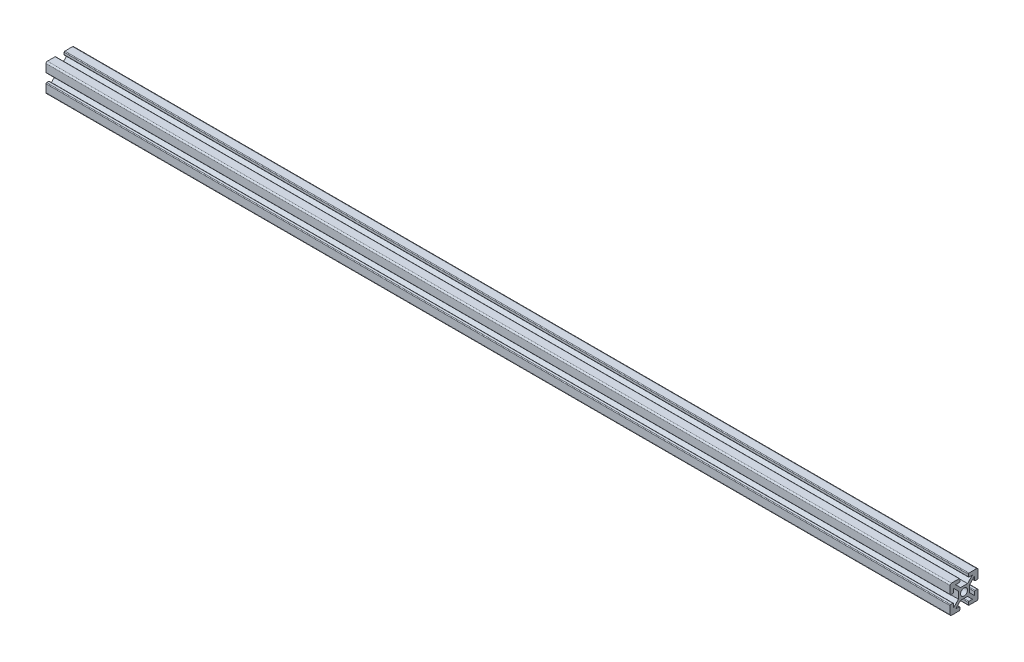
SolidWorks part; units mm, degrees
ref_plane "Front Plane" through (0, 0, 0) normal (0, 0, 1) x (1, 0, 0)
ref_plane "Top Plane" through (0, 0, 0) normal (0, 1, 0) x (1, 0, 0)
ref_plane "Right Plane" through (0, 0, 0) normal (1, 0, 0) x (0, 0, -1)
sketch "Sketch1" plane through (0, 0, 0) normal (0, 0, 1) x (1, 0, 0)
  line L0 (-263.8478, 0) -> (386.1522, 0)
  dimension "D1" = 650
other "Aluminium prof ALUMINIUM PROF(1)"
ref_plane "Plane1" through (-263.8478, 0, 0) normal (1, 0, 0) x (0, 1, 0)
sketch "Sketch11" plane through (-263.8478, 0, 0) normal (1, 0, 0) x (0, 1, 0)
  line L0 (0, 0) -> (0, 19.0058) construction
  line L9 (0, 0) -> (23.0409, 0) construction
  line L10 (23.0409, 0) -> (23.0409, -0.0585) construction
  line L11 (23.0409, -0.0585) -> (23.0409, 0) construction
  line L13 (-2.5, 4) -> (2.5, 4)
  line L14 (2.5, 4) -> (6.0355, 7.5355)
  line L15 (6.0355, 7.5355) -> (3.5355, 7.5355)
  line L16 (3.0355, 8.0355) -> (3.0355, 9.5355)
  line L17 (3.5355, 10.0355) -> (9.0355, 10.0355)
  line L18 (10.0355, 9.0355) -> (10.0355, 3.5355)
  line L19 (9.5355, 3.0355) -> (8.0355, 3.0355)
  line L20 (7.5355, 3.5355) -> (7.5355, 6.0355)
  line L21 (7.5355, 6.0355) -> (4, 2.5)
  line L22 (4, 2.5) -> (4, -2.5)
  line L23 (-10.0355, 9.0355) -> (-10.0355, 3.5355)
  line L24 (-4, 2.5) -> (-4, -2.5)
  line L25 (-7.5355, 6.0355) -> (-4, 2.5)
  line L26 (-7.5355, 3.5355) -> (-7.5355, 6.0355)
  line L27 (-9.5355, 3.0355) -> (-8.0355, 3.0355)
  line L28 (-3.5355, 10.0355) -> (-9.0355, 10.0355)
  line L29 (-3.0355, 8.0355) -> (-3.0355, 9.5355)
  line L30 (-6.0355, 7.5355) -> (-3.5355, 7.5355)
  line L31 (-2.5, 4) -> (-6.0355, 7.5355)
  line L32 (3.5355, -10.0355) -> (9.0355, -10.0355)
  line L33 (-2.5, -4) -> (-6.0355, -7.5355)
  line L34 (-6.0355, -7.5355) -> (-3.5355, -7.5355)
  line L35 (-3.0355, -8.0355) -> (-3.0355, -9.5355)
  line L36 (-3.5355, -10.0355) -> (-9.0355, -10.0355)
  line L37 (-9.5355, -3.0355) -> (-8.0355, -3.0355)
  line L38 (-7.5355, -3.5355) -> (-7.5355, -6.0355)
  line L39 (-7.5355, -6.0355) -> (-4, -2.5)
  line L40 (-10.0355, -9.0355) -> (-10.0355, -3.5355)
  line L41 (7.5355, -6.0355) -> (4, -2.5)
  line L42 (7.5355, -3.5355) -> (7.5355, -6.0355)
  line L43 (9.5355, -3.0355) -> (8.0355, -3.0355)
  line L44 (10.0355, -9.0355) -> (10.0355, -3.5355)
  line L45 (3.0355, -8.0355) -> (3.0355, -9.5355)
  line L46 (6.0355, -7.5355) -> (3.5355, -7.5355)
  line L47 (2.5, -4) -> (6.0355, -7.5355)
  line L48 (-2.5, -4) -> (2.5, -4)
  circle A0 centre (0, 0) radius 2.5
  arc A1 (-10.0355, 9.0355) -> (-9.0355, 10.0355) centre (-9.0355, 9.0355) cw
  arc A2 (-9.0355, -10.0355) -> (-10.0355, -9.0355) centre (-9.0355, -9.0355) cw
  arc A3 (9.0355, -10.0355) -> (10.0355, -9.0355) centre (9.0355, -9.0355) ccw
  arc A4 (9.0355, 10.0355) -> (10.0355, 9.0355) centre (9.0355, 9.0355) cw
  arc A5 (-9.5355, -3.0355) -> (-10.0355, -3.5355) centre (-9.5355, -3.5355) ccw
  arc A6 (-8.0355, -3.0355) -> (-7.5355, -3.5355) centre (-8.0355, -3.5355) cw
  arc A7 (-3.5355, -7.5355) -> (-3.0355, -8.0355) centre (-3.5355, -8.0355) cw
  arc A8 (-3.0355, -9.5355) -> (-3.5355, -10.0355) centre (-3.5355, -9.5355) cw
  arc A9 (3.5355, -10.0355) -> (3.0355, -9.5355) centre (3.5355, -9.5355) cw
  arc A10 (3.0355, -8.0355) -> (3.5355, -7.5355) centre (3.5355, -8.0355) cw
  arc A11 (9.5355, -3.0355) -> (10.0355, -3.5355) centre (9.5355, -3.5355) cw
  arc A12 (7.5355, -3.5355) -> (8.0355, -3.0355) centre (8.0355, -3.5355) cw
  arc A13 (10.0355, 3.5355) -> (9.5355, 3.0355) centre (9.5355, 3.5355) cw
  arc A14 (8.0355, 3.0355) -> (7.5355, 3.5355) centre (8.0355, 3.5355) cw
  arc A15 (3.5355, 7.5355) -> (3.0355, 8.0355) centre (3.5355, 8.0355) cw
  arc A16 (3.0355, 9.5355) -> (3.5355, 10.0355) centre (3.5355, 9.5355) cw
  arc A17 (-3.5355, 10.0355) -> (-3.0355, 9.5355) centre (-3.5355, 9.5355) cw
  arc A18 (-3.0355, 8.0355) -> (-3.5355, 7.5355) centre (-3.5355, 8.0355) cw
  arc A19 (-7.5355, 3.5355) -> (-8.0355, 3.0355) centre (-8.0355, 3.5355) cw
  arc A20 (-10.0355, 3.5355) -> (-9.5355, 3.0355) centre (-9.5355, 3.5355) ccw
  point P26 (0, 4)
  point P29 (-4, 0)
  point P30 (4, 0)
  point P44 (0, -4)
  point P48 (-10.0355, 10.0355)
  point P51 (-10.0355, -10.0355)
  point P54 (10.0355, -10.0355)
  point P57 (10.0355, 10.0355)
  point P60 (-10.0355, -3.0355)
  point P63 (-7.5355, -3.0355)
  point P66 (-3.0355, -7.5355)
  point P69 (-3.0355, -10.0355)
  point P72 (3.0355, -10.0355)
  point P75 (3.0355, -7.5355)
  point P78 (10.0355, -3.0355)
  point P81 (7.5355, -3.0355)
  point P84 (10.0355, 3.0355)
  point P87 (7.5355, 3.0355)
  point P90 (3.0355, 7.5355)
  point P93 (3.0355, 10.0355)
  point P96 (-3.0355, 10.0355)
  point P99 (-3.0355, 7.5355)
  point P102 (-7.5355, 3.0355)
  point P105 (-10.0355, 3.0355)
  point P106 (0, 0)
  dimension "D5" = 4
  dimension "D12" = 1
  dimension "D13" = 0.5
  dimension "D1" = 135
  dimension "D2" = 2.5
  dimension "D3" = 4
  dimension "D4" = 2.5
  dimension "D6" = 7
  dimension "D7" = 7
  dimension "D8" = 3
  dimension "D9" = 3
  dimension "D10" = 5
  dimension "D11" = 23.0409
